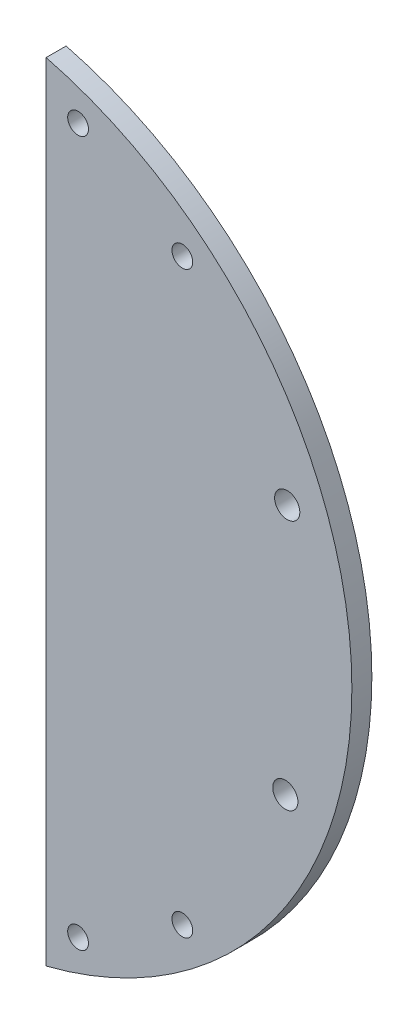
SolidWorks part; units mm, degrees
material "Acrylic (Medium-high impact)"
ref_plane "Front Plane" through (0, 0, 0) normal (0, 0, 1) x (1, 0, 0)
ref_plane "Top Plane" through (0, 0, 0) normal (0, 1, 0) x (1, 0, 0)
ref_plane "Right Plane" through (0, 0, 0) normal (1, 0, 0) x (0, 0, -1)
sketch "Sketch1" plane through (0, 0, 0) normal (0, 0, 1) x (-1, 0, 0)
  line L0 (0, 0) -> (-48.575, 0.3664) construction
  line L3 (0, -62.1367) -> (0, 62.8696)
  circle A15 centre (-5.075, 56.3664) radius 1.65
  circle A16 centre (-21.6385, 46.3664) radius 1.65
  circle A21 centre (-5.075, -55.6336) radius 1.65
  circle A22 centre (-21.6385, -45.6336) radius 1.65
  arc A23 (0, 62.8696) -> (0, -62.1367) centre (15.925, 0.3664) ccw
  circle A24 centre (-38, 20.2872) radius 2
  circle A25 centre (-38.3017, -19.7116) radius 2
  point P2 (15.925, 0.3664)
  dimension "D3" = 4
  dimension "D4" = 20
  dimension "D10" = 3.3
  dimension "D2" = 64.5
  dimension "D5" = 38
extrude "Boss-Extrude1" add sketch "Sketch1" along normal blind 3.175
